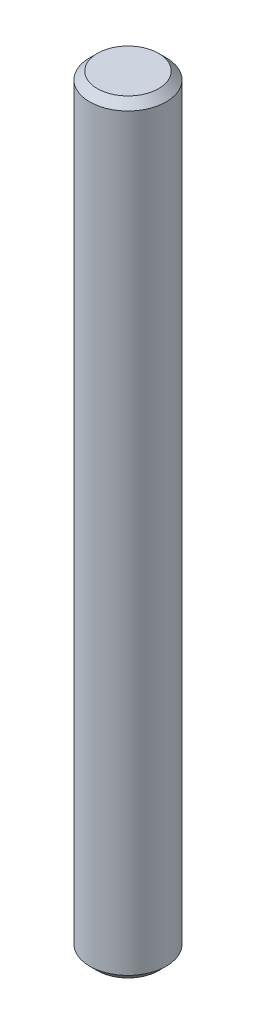
SolidWorks part; units mm, degrees
ref_plane "Front Plane" through (0, 0, 0) normal (0, 0, 1) x (1, 0, 0)
ref_plane "Top Plane" through (0, 0, 0) normal (0, 1, 0) x (1, 0, 0)
ref_plane "Right Plane" through (0, 0, 0) normal (1, 0, 0) x (0, 0, -1)
sketch "Sketch1" plane through (0, 0, 0) normal (0, 1, 0) x (1, 0, 0)
  circle A0 centre (0, 0) radius 4.005
  dimension "D1" = 8.01
extrude "Boss-Extrude1" add sketch "Sketch1" along normal blind 80
chamfer "Chamfer1" distance 0.8 angle 45 2 edges at (0, 0, 4.005) (0, 80, 4.005)
